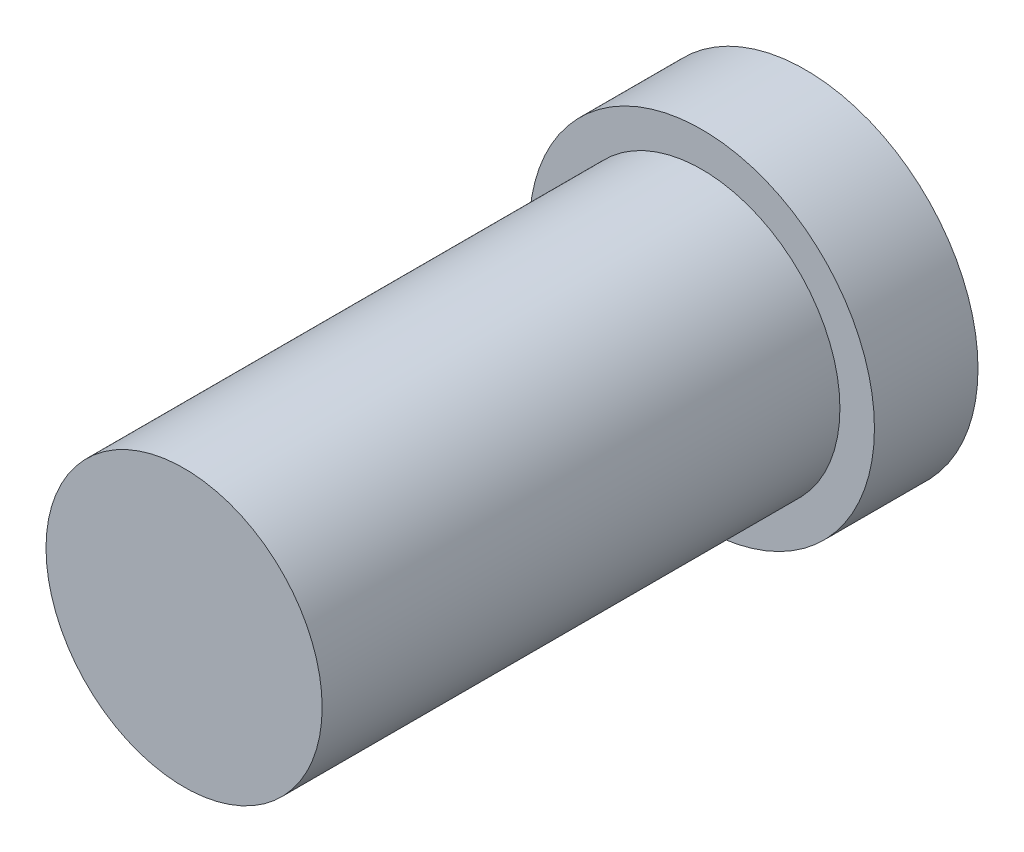
SolidWorks part; units mm, degrees
ref_plane "Front Plane" through (0, 0, 0) normal (0, 0, 1) x (1, 0, 0)
ref_plane "Top Plane" through (0, 0, 0) normal (0, 1, 0) x (1, 0, 0)
ref_plane "Right Plane" through (0, 0, 0) normal (1, 0, 0) x (0, 0, -1)
sketch "Sketch1" plane through (0, 0, 0) normal (0, 0, 1) x (1, 0, 0)
  circle A0 centre (0, 0) radius 5
  dimension "D1" = 10
extrude "Boss-Extrude1" add sketch "Sketch1" along normal blind 3
sketch "Sketch2" plane through (0, 0, 3) normal (0, 0, 1) x (1, 0, 0)
  circle A0 centre (0, 0) radius 4
  dimension "D1" = 8
extrude "Boss-Extrude2" add sketch "Sketch2" along normal blind 15
